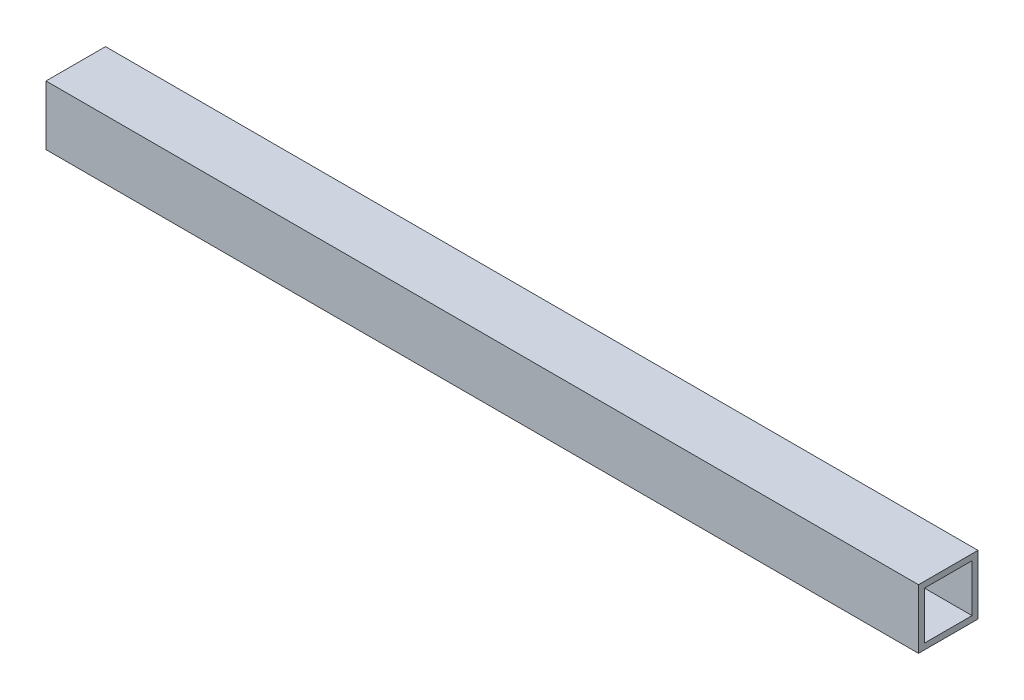
SolidWorks part; units mm, degrees
ref_plane "Front Plane" through (0, 0, 0) normal (0, 0, 1) x (1, 0, 0)
ref_plane "Top Plane" through (0, 0, 0) normal (0, 1, 0) x (1, 0, 0)
ref_plane "Right Plane" through (0, 0, 0) normal (1, 0, 0) x (0, 0, -1)
sketch "Sketch1" plane through (0, 0, 0) normal (1, 0, 0) x (0, 0, -1)
  line L0 (-6, 6) -> (6, 6)
  line L1 (-7.5, 7.5) -> (7.5, 7.5)
  line L2 (-7.5, 7.5) -> (-7.5, -7.5)
  line L3 (-7.5, -7.5) -> (7.5, -7.5)
  line L4 (7.5, 7.5) -> (7.5, -7.5)
  line L5 (-7.5, 7.5) -> (7.5, -7.5) construction
  line L6 (-7.5, -7.5) -> (7.5, 7.5) construction
  line L7 (6, 6) -> (6, -6)
  line L8 (-6, -6) -> (6, -6)
  line L9 (-6, 6) -> (-6, -6)
  point P0 (0, 0)
  dimension "D1" = 15
  dimension "D2" = 15
  dimension "D3" = 1.5
extrude "Boss-Extrude1" add sketch "Sketch1" along normal mid plane 220
sketch "Sketch2" plane through (0, 7.5, 0) normal (0, 1, 0) x (1, 0, 0)
  line L0 (0, 0) -> (110, 0) construction
  line L1 (110, 7.5) -> (110, -7.5) construction
  circle A0 centre (55, 0) radius 2
  dimension "D1" = 4
extrude "Cut-Extrude1" [suppressed] cut sketch "Sketch2" against normal through all
